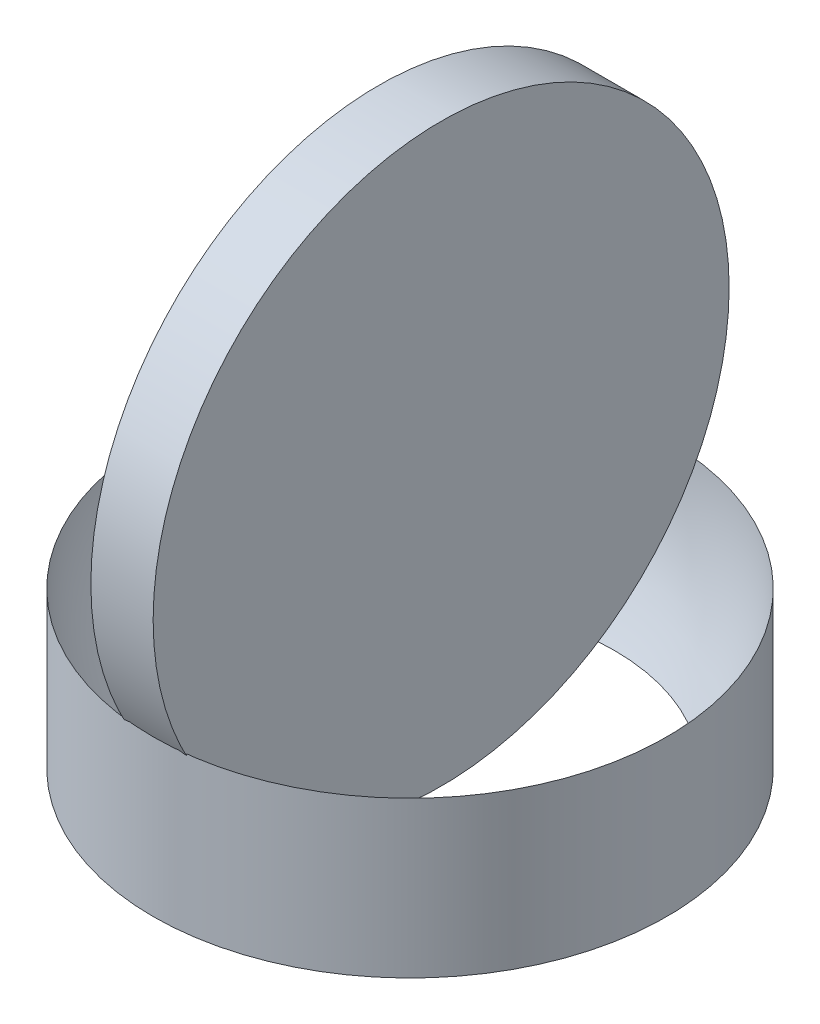
SolidWorks part; units mm, degrees
ref_plane "Alzado" through (0, 0, 0) normal (0, 0, 1) x (1, 0, 0)
ref_plane "Planta" through (0, 0, 0) normal (0, 1, 0) x (1, 0, 0)
ref_plane "Vista lateral" through (0, 0, 0) normal (1, 0, 0) x (0, 0, -1)
sketch "Croquis1" plane through (0, 0, 0) normal (0, 1, 0) x (1, 0, 0)
  circle A0 centre (0, 0) radius 8.25
  dimension "D1" = 16.5
extrude "Saliente-Extruir1" add sketch "Croquis1" along normal blind 5
sketch "Croquis3" plane through (0, 0, 0) normal (1, 0, 0) x (0, 0, -1)
  circle A0 centre (0, 9.25) radius 9.25
  dimension "D1" = 18.5
sketch "Croquis4" plane through (0, 5, 0) normal (0, 1, 0) x (1, 0, 0)
  line L0 (8.25, 0) -> (-8.25, 0)
  arc A0 (8.25, 0) -> (-8.25, 0) centre (0, 0) ccw
  circle A1 centre (0, 0) radius 8.25 construction
revolve "Cortar-Revolución3" cut sketch "Croquis4" angle 180 about L0
extrude "Saliente-Extruir3" add sketch "Croquis3" along normal mid plane 2 separate body
